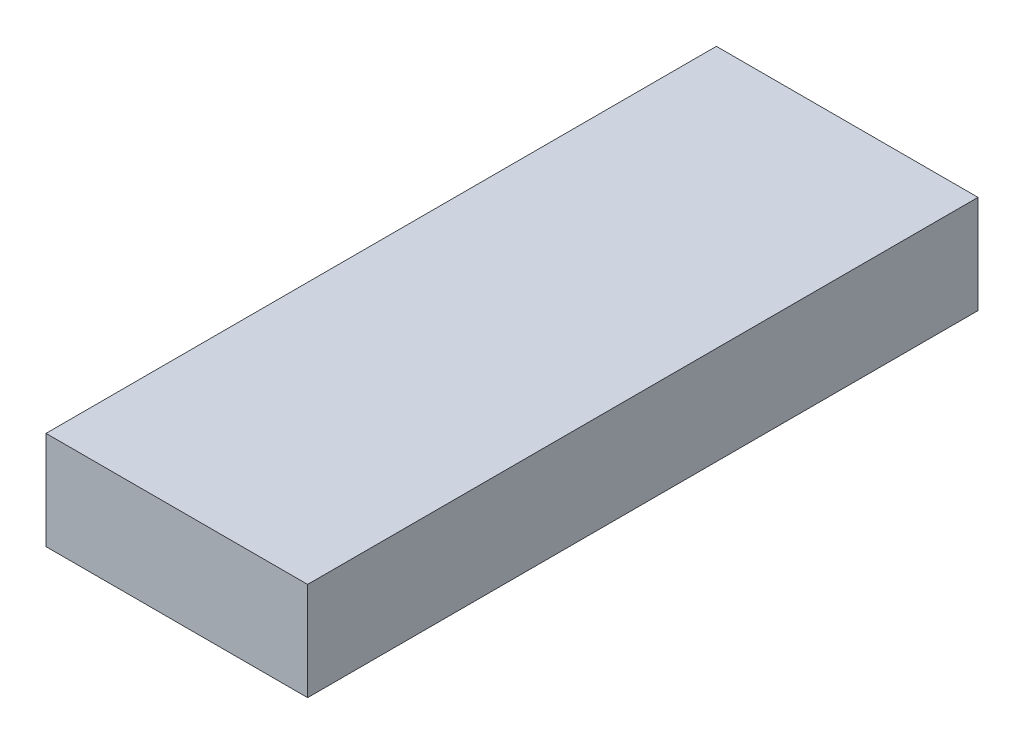
SolidWorks part; units mm, degrees
material "Простая углеродистая сталь"
ref_plane "Спереди" through (0, 0, 0) normal (0, 0, 1) x (1, 0, 0)
ref_plane "Сверху" through (0, 0, 0) normal (0, 1, 0) x (1, 0, 0)
ref_plane "Справа" through (0, 0, 0) normal (1, 0, 0) x (0, 0, -1)
sketch "Эскиз1" plane through (0, 0, 0) normal (0, 1, 0) x (1, 0, 0)
  line L1 (0, 0) -> (80, 0)
  line L2 (0, 0) -> (0, 205)
  line L3 (0, 205) -> (80, 205)
  line L4 (80, 0) -> (80, 205)
extrude "Бобышка-Вытянуть1" add sketch "Эскиз1" along normal blind 30
